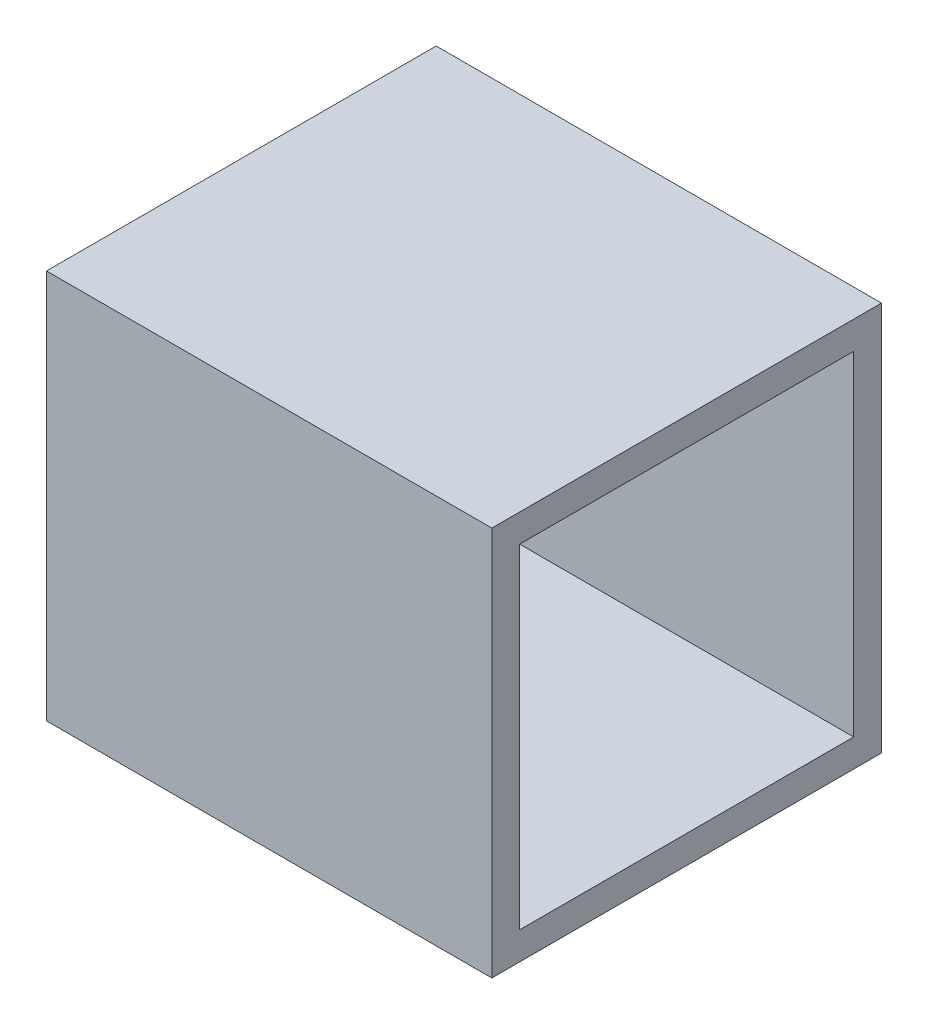
SolidWorks part; units mm, degrees
ref_plane "Front Plane" through (0, 0, 0) normal (0, 0, 1) x (1, 0, 0)
ref_plane "Top Plane" through (0, 0, 0) normal (0, 1, 0) x (1, 0, 0)
ref_plane "Right Plane" through (0, 0, 0) normal (1, 0, 0) x (0, 0, -1)
sketch "Sketch1" plane through (0, 0, 0) normal (0, 1, 0) x (1, 0, 0)
  line L1 (0, 0) -> (0.8, 0)
  line L2 (0, 0) -> (0, -0.7)
  line L3 (0, -0.7) -> (0.8, -0.7)
  line L4 (0.8, 0) -> (0.8, -0.7)
  dimension "D1" = 0.8
  dimension "D2" = 0.7
extrude "Boss-Extrude1" add sketch "Sketch1" along normal blind 0.7
sketch "Sketch2" plane through (0.8, 0, 0) normal (1, 0, 0) x (0, 0, -1)
  line L0 (-0.7, 0.7) -> (0, 0.7) construction
  line L1 (-0.65, 0.65) -> (-0.05, 0.65)
  line L2 (-0.65, 0.65) -> (-0.65, 0.05)
  line L3 (-0.65, 0.05) -> (-0.05, 0.05)
  line L4 (-0.05, 0.65) -> (-0.05, 0.05)
  line L5 (0, 0.7) -> (0, 0) construction
  point P6 (-0.35, 0.7)
  point P7 (-0.35, 0.65)
  point P10 (0, 0.35)
  point P11 (-0.05, 0.35)
  dimension "D1" = 0.6
  dimension "D2" = 0.6
extrude "Cut-Extrude1" cut sketch "Sketch2" against normal through all both and the other way through all
